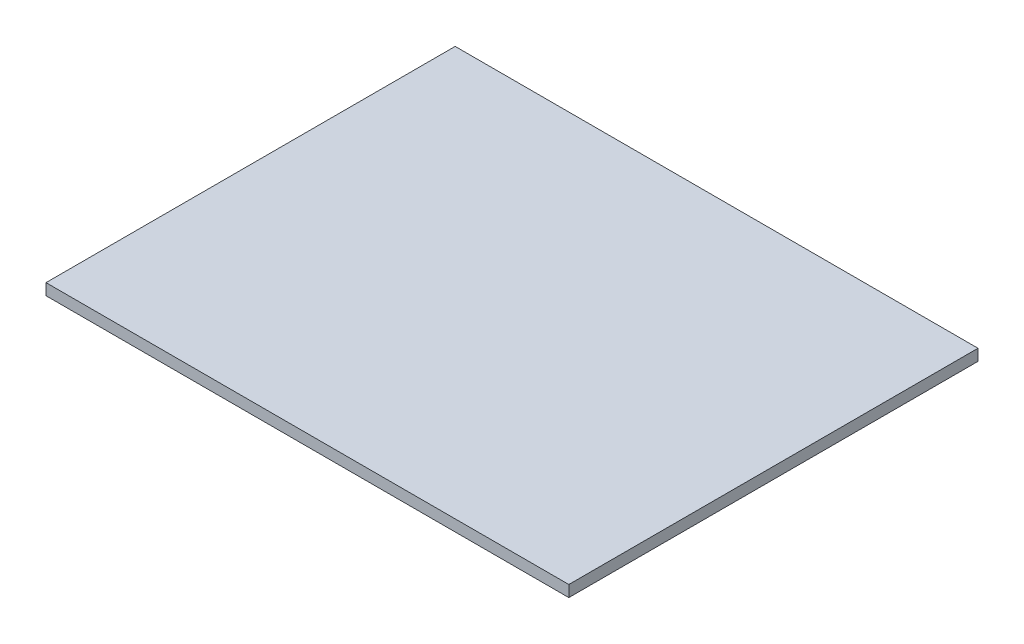
SolidWorks part; units mm, degrees
ref_plane "Plan de face" through (0, 0, 0) normal (0, 0, 1) x (1, 0, 0)
ref_plane "Plan de dessus" through (0, 0, 0) normal (0, 1, 0) x (1, 0, 0)
ref_plane "Plan de droite" through (0, 0, 0) normal (1, 0, 0) x (0, 0, -1)
sketch "Esquisse1" plane through (0, 0, 0) normal (0, 1, 0) x (1, 0, 0)
  line L1 (-23, 18) -> (23, 18)
  line L2 (-23, 18) -> (-23, -18)
  line L3 (-23, -18) -> (23, -18)
  line L4 (23, 18) -> (23, -18)
  point P4 (23, 0)
  point P7 (0, 18)
  dimension "D1" = 36
  dimension "D2" = 46
extrude "Boss.-Extru.1" add sketch "Esquisse1" along normal blind 1
